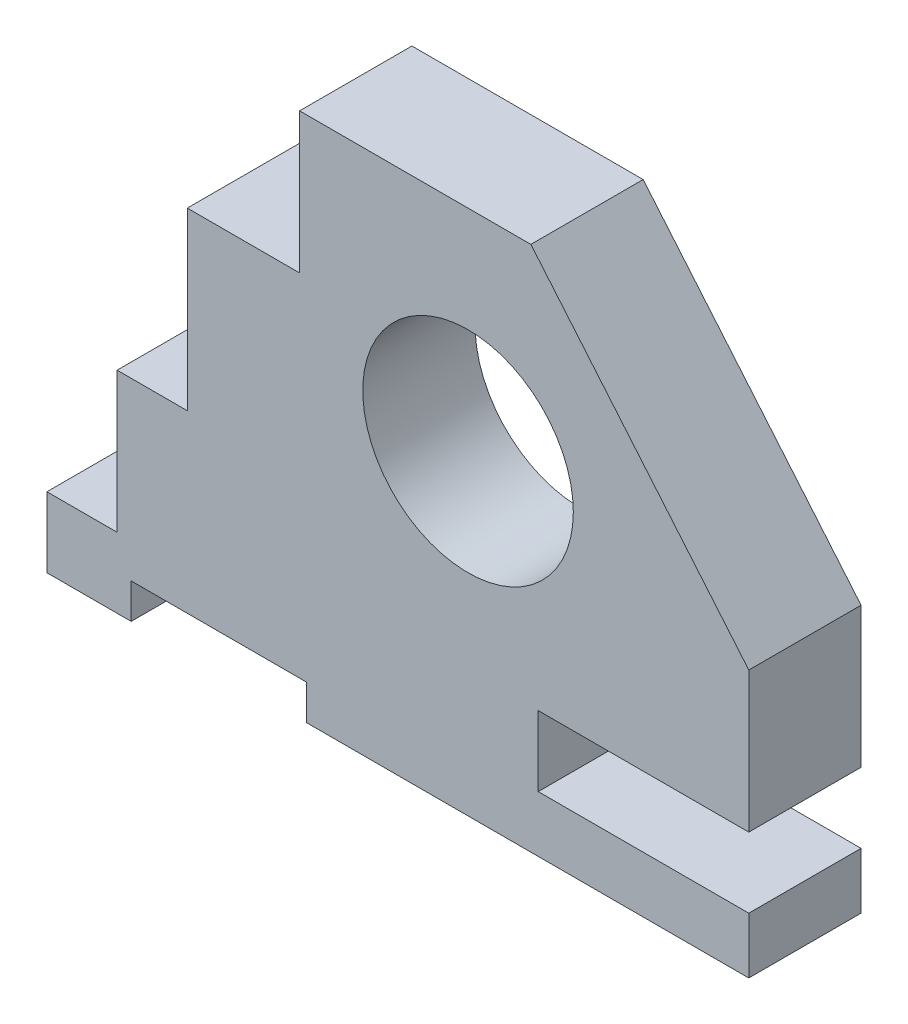
SolidWorks part; units mm, degrees
ref_plane "Front Plane" through (0, 0, 0) normal (0, 0, 1) x (1, 0, 0)
ref_plane "Top Plane" through (0, 0, 0) normal (0, 1, 0) x (1, 0, 0)
ref_plane "Right Plane" through (0, 0, 0) normal (1, 0, 0) x (0, 0, -1)
sketch "Sketch2" plane through (0, 0, 0) normal (0, 0, 1) x (1, 0, 0)
  line L0 (18.9533, 37.5) -> (50, 0.5)
  line L1 (18.9533, 37.5) -> (-14, 37.5)
  line L2 (50, 0.5) -> (50, -19.5)
  line L3 (50, -37.5) -> (-13, -37.5)
  line L4 (-50, -27.5) -> (-50, -37.5)
  line L8 (-38, -37.5) -> (-38, -32.5)
  line L9 (-38, -32.5) -> (-13, -32.5)
  line L10 (-13, -37.5) -> (-13, -32.5)
  line L13 (-30, 17.5) -> (-14, 17.5)
  line L14 (-14, 37.5) -> (-14, 17.5)
  line L17 (-40, -7.5) -> (-30, -7.5)
  line L18 (-30, 17.5) -> (-30, -7.5)
  line L21 (-50, -27.5) -> (-40, -27.5)
  line L22 (-40, -7.5) -> (-40, -27.5)
  line L23 (50, -29.5) -> (50, -37.5)
  line L24 (20, -29.5) -> (50, -29.5)
  line L25 (20, -29.5) -> (20, -19.5)
  line L26 (20, -19.5) -> (50, -19.5)
  line L28 (-38, -37.5) -> (-50, -37.5)
  circle A0 centre (10, 7.5) radius 15
  point P0 (0, 0)
  dimension "D11" = 30
  dimension "D12" = 40
  dimension "D1" = 100
  dimension "D2" = 36
  dimension "D3" = 25
  dimension "D4" = 5
  dimension "D5" = 20
  dimension "D6" = 20
  dimension "D7" = 10
  dimension "D8" = 10
  dimension "D9" = 30
  dimension "D10" = 55
  dimension "D13" = 8
  dimension "D14" = 10
  dimension "D15" = 38
  dimension "D16" = 45
  dimension "D17" = 30
  dimension "D18" = 12
  dimension "D19" = 75
  dimension "D20" = 40
extrude "Boss-Extrude1" add sketch "Sketch2" along normal blind 16
